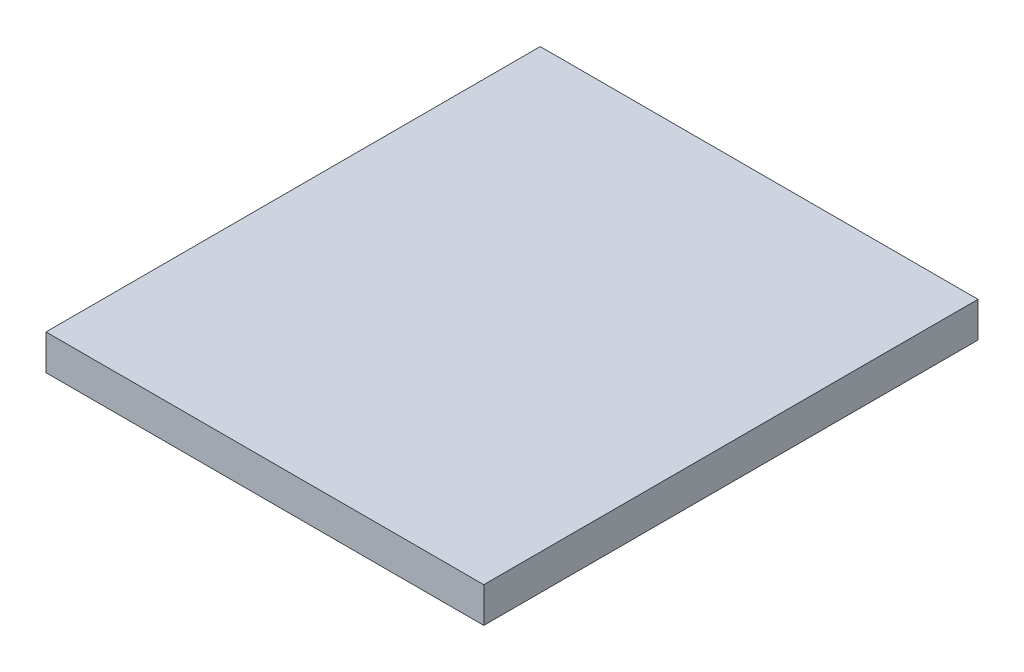
SolidWorks part; units mm, degrees
material "PPS"
ref_plane "Płaszczyzna XY" through (0, 0, 0) normal (0, 0, 1) x (1, 0, 0)
ref_plane "Płaszczyzna XZ" through (0, 0, 0) normal (0, 1, 0) x (1, 0, 0)
ref_plane "Płaszczyzna YZ" through (0, 0, 0) normal (1, 0, 0) x (0, 0, -1)
sketch "Szkic1" plane through (0, 0, 0) normal (0, 1, 0) x (1, 0, 0)
  line L0 (0, 0) -> (0, -140)
  line L1 (0, -140) -> (124, -140)
  line L2 (124, -140) -> (124, 0)
  line L3 (124, 0) -> (0, 0)
  dimension "D1" = 140
  dimension "D2" = 124
  dimension "D3" = 140
  dimension "D4" = 0
extrude "Dodanie-wyciągnięcie1" add sketch "Szkic1" along normal blind 1
sketch "Szkic2" plane through (0, 0, 0) normal (0, -1, 0) x (1, 0, 0)
  line L0 (124, 0) -> (0, 0)
  line L1 (124, 0) -> (0, 0) construction
  line L2 (0, 0) -> (0, 2)
  line L3 (0, 0) -> (0, 140) construction
  line L4 (0, 2) -> (124, 2)
  line L5 (124, 140) -> (124, 0) construction
  line L6 (124, 2) -> (124, 0)
  dimension "D1" = 2
sketch "Szkic3" plane through (0, 1, 0) normal (0, 1, 0) x (1, 0, 0)
  line L0 (0, 0) -> (0, -140)
  line L1 (0, 0) -> (0, -140) construction
  line L2 (0, -140) -> (124, -140) construction
  line L3 (0, -140) -> (124, -140)
  line L4 (124, -140) -> (124, 0) construction
  line L5 (124, -140) -> (124, 0)
  line L6 (124, 0) -> (0, 0) construction
  line L7 (124, 0) -> (123, 0)
  line L8 (123, 0) -> (123, -139)
  line L9 (123, -139) -> (1, -139)
  line L10 (1, -139) -> (1, 0)
  line L11 (1, 0) -> (0, 0)
  dimension "D1" = 1
  dimension "D2" = 1
  dimension "D3" = 1
extrude "Dodanie-wyciągnięcie2" add sketch "Szkic3" against normal blind 10
